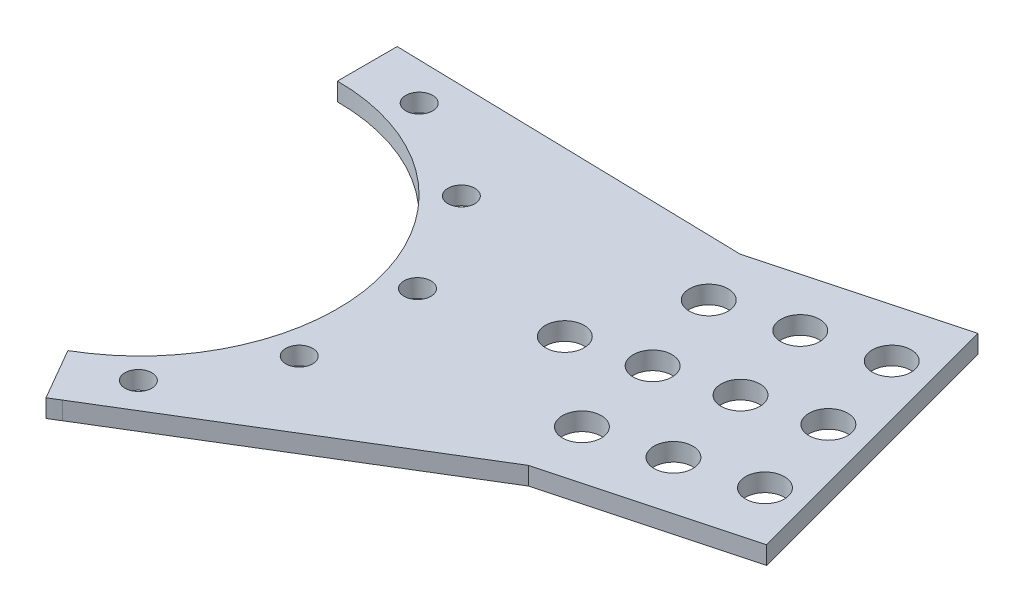
SolidWorks part; units mm, degrees
ref_plane "Front Plane" through (0, 0, 0) normal (0, 0, 1) x (1, 0, 0)
ref_plane "Top Plane" through (0, 0, 0) normal (0, 1, 0) x (1, 0, 0)
ref_plane "Right Plane" through (0, 0, 0) normal (1, 0, 0) x (0, 0, -1)
sketch "Sketch1" plane through (0, 0, 0) normal (0, 1, 0) x (1, 0, 0)
  line L0 (0, 33) -> (0, 43)
  line L1 (16.5, -28.5788) -> (21.5, -37.2391)
  arc A0 (0, 43) -> (21.5, -37.2391) centre (0, 0) cw
  arc A1 (0, 33) -> (16.5, -28.5788) centre (0, 0) cw
  dimension "D1" = 150
  dimension "D2" = 33
  dimension "D3" = 43
extrude "Boss-Extrude1" add sketch "Sketch1" along normal mid plane 3
sketch "Sketch4" plane through (0, 0, 0) normal (0, 1, 0) x (1, 0, 0)
  line L0 (0, 0) -> (64.2341, 17.2115) construction
  line L1 (90.1221, 50.0301) -> (25.4051, 32.6892)
  line L2 (90.1221, 50.0301) -> (103.0631, 1.7338)
  line L3 (25.4051, 32.6892) -> (38.346, -15.6071)
  line L4 (103.0631, 1.7338) -> (38.346, -15.6071)
  line L5 (31.8756, 8.541) -> (96.5926, 25.8819) construction
  line L6 (57.7636, 41.3596) -> (70.7045, -6.9367) construction
  line L7 (0, 43) -> (0, 33) construction
  arc A1 (16.5, -28.5788) -> (0, 33) centre (0, 0) ccw construction
  dimension "D1" = 75
  dimension "D2" = 100
  dimension "D3" = 50
extrude "Boss-Extrude2" add sketch "Sketch4" along normal mid plane 3
sketch "Sketch5" plane through (0, 0, 0) normal (0, 1, 0) x (1, 0, 0)
  line L0 (0, 0) -> (96.5926, 25.8819) construction
  line L1 (103.0631, 1.7338) -> (90.1221, 50.0301) construction
  line L2 (0, 43) -> (58.7226, 41.6166)
  line L3 (90.1221, 50.0301) -> (27.3231, 33.2031) construction
  line L4 (58.7226, 41.6166) -> (27.3231, 33.2031)
  line L5 (27.3231, 33.2031) -> (0, 43)
  line L6 (71.6636, -6.6797) -> (40.2641, -15.0932)
  line L7 (21.5, -37.2391) -> (71.6636, -6.6797)
  line L8 (40.2641, -15.0932) -> (21.5, -37.2391)
extrude "Boss-Extrude3" add sketch "Sketch5" along normal mid plane 3
sketch "Sketch2" plane through (0, 1.5, 0) normal (0, 1, 0) x (1, 0, 0)
  arc A0 (18.6469, -33.1103) -> (0, 38) centre (0, 0) ccw construction
  circle A1 centre (36.7573, 9.6387) radius 2.25
  dimension "D1" = 4.5
  dimension "D2" = 38
extrude "Cut-Extrude1" cut sketch "Sketch2" against normal through all both and the other way through all
pattern_circular "CirPattern1" count 3 every 30 about axis through (0, 0, 0) along (0, 1, 0) of "Cut-Extrude1"
sketch "Sketch6" plane through (0, 1.5, 0) normal (0, 1, 0) x (1, 0, 0)
  line L0 (0, 0) -> (96.5926, 25.8819) construction
  line L1 (103.0631, 1.7338) -> (90.1221, 50.0301) construction
  line L2 (86.9147, 38.8179) -> (94.6793, 9.8401) construction
  circle A0 centre (94.6793, 9.8401) radius 3.25
  circle A1 centre (86.9147, 38.8179) radius 3.25
  point P8 (90.797, 24.329)
  dimension "D1" = 6.5
  dimension "D2" = 30
  dimension "D3" = 6
extrude "Cut-Extrude2" cut sketch "Sketch6" against normal through all both and the other way through all
pattern_linear "LPattern1" count 3 spacing 12.5 along (-0.9659, 0, 0.2588) of "Cut-Extrude2"
sketch "Sketch7" plane through (0, 1.5, 0) normal (0, 1, 0) x (1, 0, 0)
  line L0 (0, 0) -> (96.5926, 25.8819) construction
  line L1 (103.0631, 1.7338) -> (90.1221, 50.0301) construction
  circle A0 centre (90.797, 24.329) radius 3.25
  dimension "D1" = 6.5
  dimension "D2" = 6
extrude "Cut-Extrude3" cut sketch "Sketch7" against normal blind 10
pattern_linear "LPattern2" count 4 spacing 12 along (-0.9659, 0, 0.2588) of "Cut-Extrude3"
